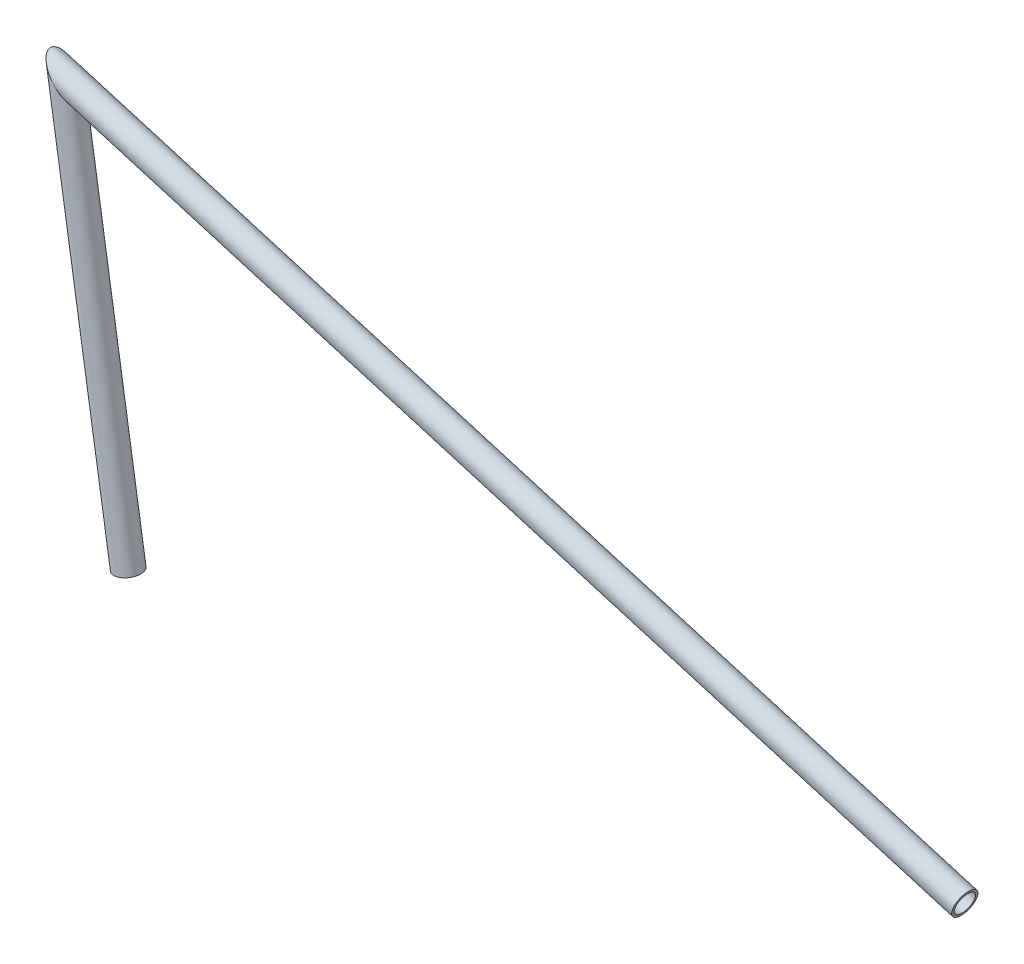
SolidWorks part; units mm, degrees
ref_plane "Front" through (0, 0, 0) normal (0, 0, 1) x (1, 0, 0)
ref_plane "Top" through (0, 0, 0) normal (0, 1, 0) x (1, 0, 0)
ref_plane "Right" through (0, 0, 0) normal (1, 0, 0) x (0, 0, -1)
sketch "Sketch1" plane through (0, 0, 0) normal (0, 0, 1) x (1, 0, 0)
  line L1 (-38.1, 0) -> (-38.1, -259.1924) construction
  line L2 (38.9, -247.3423) -> (-75.273, 11.8495)
  line L4 (0, 0) -> (21.0109, -31.7829) construction
  line L5 (562.7765, -166.7188) -> (-38.1, -259.1924) construction
  line L6 (6.5066, -41.3714) -> (47.7089, -14.1334) construction
  line L7 (0, 0) -> (0, 537.8337) construction
  line L8 (0, 0) -> (562.7765, -166.7188)
  line L10 (38.9, -247.3423) -> (0, 0)
  line L11 (562.7765, -166.7188) -> (562.7765, 34.408) construction
  line L12 (-38.1, 0) -> (38.9, -247.3423) construction
  line L14 (-443.1085, -259.1924) -> (876.7207, -259.1924) construction
  circle A0 centre (562.7765, -166.7188) radius 14.6812 construction
  circle A1 centre (38.9, -247.3423) radius 14.6812 construction
  dimension "D8" = 29.3624
  dimension "D9" = 29.3624
  dimension "D1" = 24.53
  dimension "D2" = 77
  dimension "D3" = 38.1
  dimension "D4" = 250.3826
  dimension "D5" = 38.1
  dimension "D6" = 73.498
  dimension "D7" = 92.4737
  dimension "D10" = 76.2
  dimension "D11" = 11.8501
  dimension "D12" = 259.1918
other "Structural Member1"
ref_plane "Plane1" through (38.9, -247.3423, 0) normal (-0.1554, 0.9879, 0) x (-0.9879, -0.1554, 0)
sketch "Sketch11" plane through (38.9, -247.3423, 0) normal (-0.1554, 0.9879, 0) x (-0.9879, -0.1554, 0)
  circle A0 centre (0, 0) radius 6.4643
  circle A1 centre (0, 0) radius 7.9375
  point P5 (0, 0)
  dimension "Out_dia" = 15.875
  dimension "D1" = 1.4732
sketch3d "3DSketch1"
  line L0 (21.0109, -31.7829, 0) -> (21.0109, -31.7829, -25.4) construction
  dimension "D1" = 25.4
